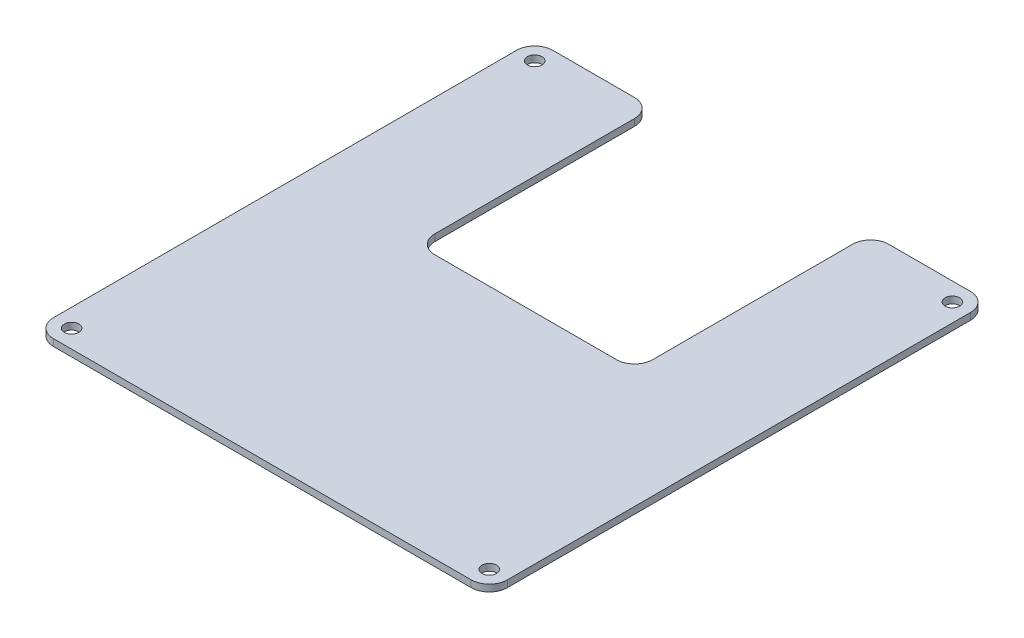
SolidWorks part; units mm, degrees
ref_plane "Front Plane" through (0, 0, 0) normal (0, 0, 1) x (1, 0, 0)
ref_plane "Top Plane" through (0, 0, 0) normal (0, 1, 0) x (1, 0, 0)
ref_plane "Right Plane" through (0, 0, 0) normal (1, 0, 0) x (0, 0, -1)
sketch "Sketch1" plane through (0, 0, 0) normal (0, 1, 0) x (1, 0, 0)
  line L1 (-50, -55) -> (50, -55)
  line L2 (-50, -55) -> (-50, 55)
  line L3 (-50, 55) -> (50, 55)
  line L4 (50, -55) -> (50, 55)
  line L5 (-50, -55) -> (50, 55) construction
  line L6 (-50, 55) -> (50, -55) construction
  point P0 (0, 0)
extrude "Boss-Extrude1" add sketch "Sketch1" along normal blind 1.5
sketch "Sketch2" plane through (0, 0, 0) normal (0, -1, 0) x (-1, 0, 0)
  line L0 (0, 55) -> (-24, 55)
  line L1 (-50, 55) -> (50, 55) construction
  line L2 (-24, 55) -> (-24, 3)
  line L3 (0, 55) -> (24, 55)
  line L4 (24, 55) -> (24, 3)
  line L5 (24, 3) -> (-24, 3)
extrude "Cut-Extrude1" cut sketch "Sketch2" against normal blind 10
fillet "Fillet1" radius 4 8 edges at (50, 0.75, -55) (-50, 0.75, -55) (50, 0.75, 55) (-50, 0.75, 55) (24, 0.75, -3) (-24, 0.75, -3) (-24, 0.75, -55) (24, 0.75, -55)
sketch "Sketch4" plane through (0, 0, 0) normal (0, -1, 0) x (-1, 0, 0)
  circle A0 centre (46, -51) radius 1.6
  circle A1 centre (46, 51) radius 1.6
  circle A2 centre (-46, 51) radius 1.6
  circle A3 centre (-46, -51) radius 1.6
extrude "Cut-Extrude2" cut sketch "Sketch4" against normal blind 10
